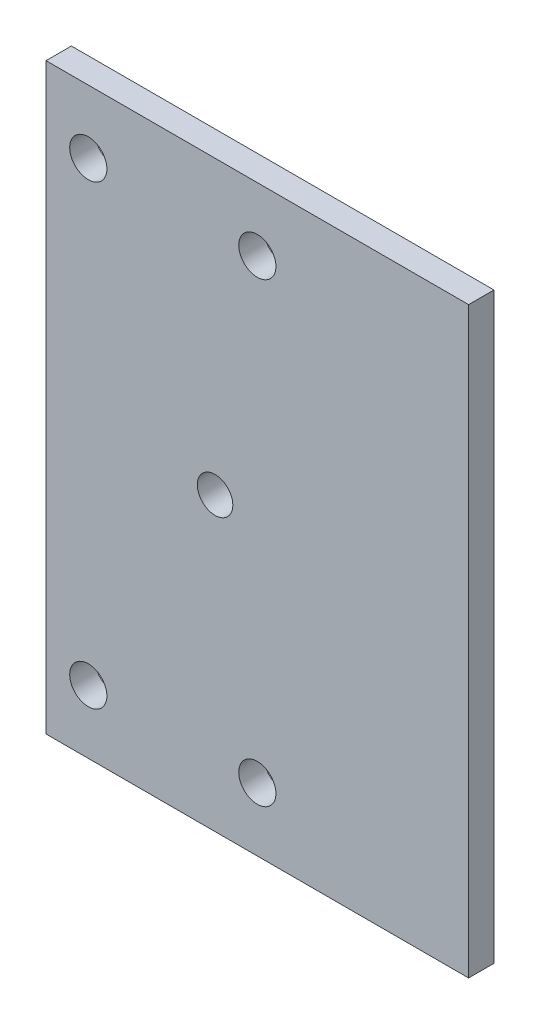
SolidWorks part; units mm, degrees
ref_plane "正面" through (0, 0, 0) normal (0, 0, 1) x (1, 0, 0)
ref_plane "平面" through (0, 0, 0) normal (0, 1, 0) x (1, 0, 0)
ref_plane "右側面" through (0, 0, 0) normal (1, 0, 0) x (0, 0, -1)
sketch "ｽｹｯﾁ1" plane through (0, 0, 0) normal (0, 0, 1) x (1, 0, 0)
  line L1 (-20, 14.5) -> (20, 14.5)
  line L2 (-20, 14.5) -> (-20, -14.5)
  line L3 (-20, -14.5) -> (20, -14.5)
  line L4 (20, 14.5) -> (20, -14.5)
  line L5 (-20, 14.5) -> (20, -14.5) construction
  line L6 (-20, -14.5) -> (20, 14.5) construction
  point P0 (0, 0)
  dimension "D1" = 29
  dimension "D2" = 40
extrude "ﾎﾞｽ - 押し出し1" add sketch "ｽｹｯﾁ1" along normal blind 3
sketch "ｽｹｯﾁ3" plane through (0, -14.5, 0) normal (0, -1, 0) x (-1, 0, 0)
  line L0 (20, 0) -> (-20, 0) construction
  line L1 (20, -3) -> (-20, -3)
  line L2 (20, -3) -> (20, 0)
  line L3 (20, 0) -> (-20, 0)
  line L4 (-20, -3) -> (-20, 0)
extrude "ﾎﾞｽ - 押し出し2" add sketch "ｽｹｯﾁ3" along normal blind 3
sketch "ｽｹｯﾁ4" plane through (0, 14.5, 0) normal (0, 1, 0) x (1, 0, 0)
  line L1 (20, -3) -> (-20, -3)
  line L2 (20, -3) -> (20, 0)
  line L3 (20, 0) -> (-20, 0)
  line L4 (-20, -3) -> (-20, 0)
extrude "ﾎﾞｽ - 押し出し3" add sketch "ｽｹｯﾁ4" along normal blind 3
sketch "ｽｹｯﾁ5" plane through (0, -17.5, 0) normal (0, -1, 0) x (1, 0, 0)
  line L1 (20, 3) -> (-20, 3)
  line L2 (20, 3) -> (20, 0)
  line L3 (20, 0) -> (-20, 0)
  line L4 (-20, 3) -> (-20, 0)
extrude "ﾎﾞｽ - 押し出し4" add sketch "ｽｹｯﾁ5" along normal blind 7
sketch "ｽｹｯﾁ6" plane through (0, 17.5, 0) normal (0, 1, 0) x (1, 0, 0)
  line L1 (-20, -3) -> (20, -3)
  line L2 (-20, -3) -> (-20, 0)
  line L3 (-20, 0) -> (20, 0)
  line L4 (20, -3) -> (20, 0)
extrude "ﾎﾞｽ - 押し出し5" add sketch "ｽｹｯﾁ6" along normal blind 7
sketch "ｽｹｯﾁ7" plane through (0, 24.5, 0) normal (0, 1, 0) x (1, 0, 0)
  line L1 (-20, -3) -> (20, -3)
  line L2 (-20, -3) -> (-20, 0)
  line L3 (-20, 0) -> (20, 0)
  line L4 (20, -3) -> (20, 0)
extrude "ﾎﾞｽ - 押し出し6" add sketch "ｽｹｯﾁ7" along normal blind 10
sketch "ｽｹｯﾁ8" plane through (0, -24.5, 0) normal (0, -1, 0) x (1, 0, 0)
  line L1 (20, 3) -> (-20, 3)
  line L2 (20, 3) -> (20, 0)
  line L3 (20, 0) -> (-20, 0)
  line L4 (-20, 3) -> (-20, 0)
extrude "ﾎﾞｽ - 押し出し7" add sketch "ｽｹｯﾁ8" along normal blind 10
sketch "ｽｹｯﾁ9" plane through (0, 0, 3) normal (0, 0, 1) x (1, 0, 0)
  line L0 (20, 34.5) -> (20, 27)
  line L1 (20, -34.5) -> (20, 34.5) construction
  line L2 (20, 27) -> (15, 27)
  line L3 (-20, 34.5) -> (-20, 27)
  line L4 (-20, 34.5) -> (-20, -34.5) construction
  line L5 (-20, 27) -> (-15, 27)
  circle A0 centre (15, 27) radius 2.2
  circle A1 centre (-15, 27) radius 2.2
  dimension "D5" = 4.4
  dimension "D6" = 4.4
  dimension "D1" = 7.5
  dimension "D2" = 5
  dimension "D3" = 7.5
  dimension "D4" = 5
sketch "ｽｹｯﾁ10" plane through (0, 0, 3) normal (0, 0, 1) x (1, 0, 0)
  line L0 (20, -34.5) -> (20, -27)
  line L1 (20, -34.5) -> (20, 34.5) construction
  line L2 (20, -27) -> (15, -27)
  line L3 (20, -27) -> (-15, -27)
  circle A0 centre (15, -27) radius 2.2
  circle A1 centre (-15, -27) radius 2.2
  dimension "D4" = 4.4
  dimension "D5" = 4.4
  dimension "D1" = 7.5
  dimension "D2" = 5
  dimension "D3" = 35
sketch "ｽｹｯﾁ11" plane through (20, 0, 0) normal (1, 0, 0) x (0, 0, -1)
  line L1 (0, 34.5) -> (-3, 34.5)
  line L2 (0, 34.5) -> (0, -34.5)
  line L3 (0, -34.5) -> (-3, -34.5)
  line L4 (-3, 34.5) -> (-3, -34.5)
  line L5 (-3, 34.5) -> (0, 34.5)
  line L6 (-3, 34.5) -> (-3, -34.5)
  line L7 (-3, -34.5) -> (0, -34.5)
  line L8 (0, 34.5) -> (0, -34.5)
sketch "ｽｹｯﾁ12" plane through (-20, 0, 0) normal (-1, 0, 0) x (0, 0, 1)
  line L1 (3, 34.5) -> (0, 34.5)
  line L2 (3, 34.5) -> (3, -34.5)
  line L3 (3, -34.5) -> (0, -34.5)
  line L4 (0, 34.5) -> (0, -34.5)
extrude "ﾎﾞｽ - 押し出し9" add sketch "ｽｹｯﾁ12" along normal blind 30
sketch "ｽｹｯﾁ15" plane through (0, 0, 3) normal (0, 0, 1) x (1, 0, 0)
  line L0 (-50, 0) -> (-10, 0)
  line L1 (-50, -34.5) -> (-50, 34.5) construction
  circle A0 centre (-10, 0) radius 2.1
  dimension "D2" = 4.2
  dimension "D1" = 40
extrude "ｶｯﾄ - 押し出し4" cut sketch "ｽｹｯﾁ15" against normal blind 10
sketch "ｽｹｯﾁ16" plane through (-50, 0, 0) normal (-1, 0, 0) x (0, 0, 1)
  line L1 (3, -34.5) -> (0, -34.5)
  line L2 (3, -34.5) -> (3, 34.5)
  line L3 (3, 34.5) -> (0, 34.5)
  line L4 (0, -34.5) -> (0, 34.5)
extrude "ｶｯﾄ - 押し出し5" cut sketch "ｽｹｯﾁ16" against normal blind 20
sketch "ｽｹｯﾁ17" plane through (0, 0, 0) normal (0, 0, -1) x (-1, 0, 0)
  line L0 (-20, 34.5) -> (-20, 27)
  line L1 (-20, 34.5) -> (-20, -34.5) construction
  line L2 (-20, 27) -> (5, 27)
  line L3 (5, 27) -> (25, 27)
  line L4 (-20, -34.5) -> (-20, -27)
  line L5 (-20, -27) -> (5, -27)
  line L6 (5, -27) -> (25, -27)
  circle A0 centre (5, 27) radius 2.2
  circle A1 centre (25, 27) radius 2.2
  circle A2 centre (5, -27) radius 2.2
  circle A3 centre (25, -27) radius 2.2
  dimension "D6" = 4.4
  dimension "D7" = 4.4
  dimension "D8" = 4.4
  dimension "D9" = 4.4
  dimension "D1" = 7.5
  dimension "D2" = 25
  dimension "D3" = 20
  dimension "D4" = 25
  dimension "D5" = 20
  dimension "D10" = 7.5
extrude "ｶｯﾄ - 押し出し6" cut sketch "ｽｹｯﾁ17" against normal blind 10
